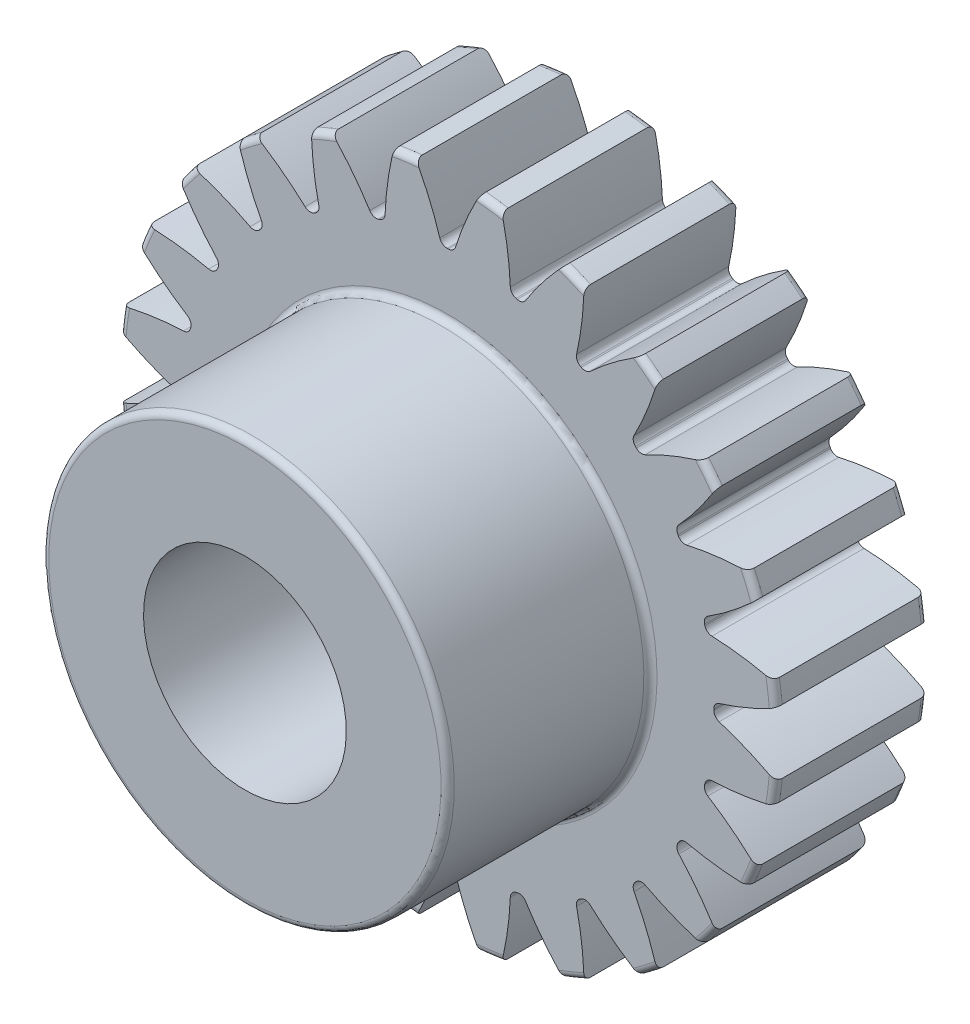
SolidWorks part; units mm, degrees
ref_plane "Front Plane" through (0, 0, 0) normal (0, 0, 1) x (1, 0, 0)
ref_plane "Top Plane" through (0, 0, 0) normal (0, 1, 0) x (1, 0, 0)
ref_plane "Right Plane" through (0, 0, 0) normal (1, 0, 0) x (0, 0, -1)
sketch "Sketch1" plane through (0, 0, 0) normal (0, 0, 1) x (1, 0, 0)
  line L0 (-304.8, 0) -> (304.8, 0) construction
  circle A0 centre (0, 0) radius 6.5 construction
  circle A1 centre (0, 0) radius 6 construction
  circle A2 centre (0, 0) radius 5.25 construction
  circle A3 centre (0, 0) radius 4 construction
  circle A4 centre (0, 0) radius 2 construction
  dimension "D2" = 0.5
  dimension "D3" = 1.25
  dimension "D1" = 1.25
sketch "Sketch2" plane through (0, 0, 0) normal (1, 0, 0) x (0, 0, -1)
  line L0 (0, 0) -> (-3, 0) construction
  line L1 (-3, 0) -> (-7, 0) construction
  dimension "Overall Width" = 7
  dimension "Face Width" = 3
sketch "Sketch4" plane through (0, 0, 0) normal (1, 0, 0) x (0, 0, -1)
  line L0 (-7, 2) -> (-7, 4)
  line L1 (-7, 4) -> (-3, 4)
  line L2 (-3, 4) -> (-3, 6.5)
  line L3 (-3, 6.5) -> (0, 6.5)
  line L4 (0, 6.5) -> (0, 2)
  line L5 (-3, 4) -> (-3, 0) construction
  line L6 (0, 6.5) -> (0, -6.5) construction
  line L7 (-3, 4) -> (0, 4) construction
  line L12 (-7, 2) -> (0, 2)
revolve "Revolve1" add sketch "Sketch4" angle 360 about L1
fillet "Fillet2" radius 0.13 4 edges at (0, 4, 7) (0, 4, 3) (0, 6.5, 3) (0, 6.5, 0)
sketch "Sketch7" plane through (0, 0, 3) normal (0, 0, 1) x (1, 0, 0)
  line L0 (0, 0) -> (0, 6.5) construction
  line L1 (0.3924, 5.9872) -> (0.6056, 6.4717) construction
  line L3 (0.8484, 6.4444) -> (0.7832, 5.9487) construction
  line L4 (0.7832, 5.9487) -> (0.6853, 5.2051) construction
  line L5 (0, 0) -> (0.6853, 5.2051) construction
  line L6 (0.3924, 5.9872) -> (0, 0) construction
  line L7 (0.3924, 5.9872) -> (0.4251, 6.4861) construction
  line L8 (0.3924, 5.9872) -> (0, 0) construction
  circle A0 centre (0, 0) radius 6.5 construction
  arc A1 (-0.0123, 5.25) -> (0.0123, 5.25) centre (0, 0) cw
  circle A2 centre (0, 0) radius 5.25 construction
  arc A3 (-0.3924, 5.9872) -> (0.3924, 5.9872) centre (0, 0) cw construction
  circle A4 centre (0, 0) radius 6 construction
  arc A5 (1.065, 6.4122) -> (0.6309, 6.4693) centre (0, 0) ccw construction
  arc A6 (0.3924, 5.9872) -> (1.1705, 5.8847) centre (0, 0) cw construction
  arc A7 (-0.6309, 6.4693) -> (0.6309, 6.4693) centre (0, 0) cw
  arc A8 (0.1559, 5.3554) -> (0.6309, 6.4693) centre (5.8843, 3.5707) cw
  arc A9 (-0.1559, 5.3554) -> (-0.6309, 6.4693) centre (-5.8843, 3.5707) ccw
  arc A10 (-0.0123, 5.25) -> (-0.1559, 5.3554) centre (-0.0126, 5.4) cw
  arc A11 (0.0123, 5.25) -> (0.1559, 5.3554) centre (0.0126, 5.4) ccw
  point P26 (-0.1237, 5.2485)
  point P29 (0.1237, 5.2485)
  dimension "D4" = 0.15
  dimension "D5" = 6
  dimension "D3" = 20
  dimension "D1" = 1.5708
  dimension "D2" = 0.7854
extrude "Cut-Extrude2" cut sketch "Sketch7" against normal through all
pattern_circular "CirPattern1" count 24 over 360 about axis through (0, 0, 0) along (0, 0, 1) of "Cut-Extrude2"
equation "\"D1@Sketch1\"=2.5*(\"Pitch Dia.@Sketch1\"/\"Number of Teeth@Sketch1\")"
equation "\"D1@CirPattern1\"=\"Number of Teeth@Sketch1\""
equation "\"D1@Fillet2\"=\"OD@Sketch1\"*.01"
equation "\"D1@Sketch7\"=3.14159*(\"Pitch Dia.@Sketch1\"/\"Number of Teeth@Sketch1\")"
equation "\"D2@Sketch7\"=\"D1@Sketch7\"/2"
equation "\"D4@Sketch7\"=\"D1@Sketch7\"*.0955"
equation "\"D5@Sketch7\"=\"Pitch Dia.@Sketch1\"/2"
